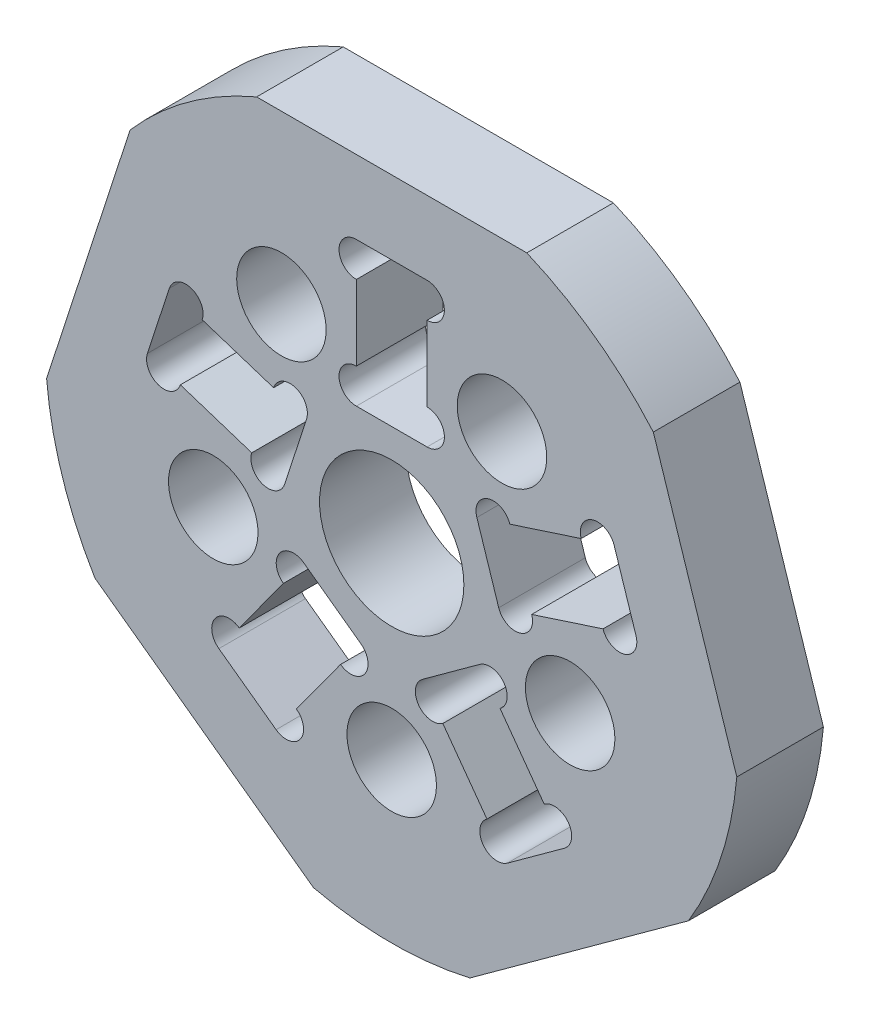
SolidWorks part; units mm, degrees
ref_plane "前视基准面" through (0, 0, 0) normal (0, 0, 1) x (1, 0, 0)
ref_plane "上视基准面" through (0, 0, 0) normal (0, 1, 0) x (1, 0, 0)
ref_plane "右视基准面" through (0, 0, 0) normal (1, 0, 0) x (0, 0, -1)
sketch "草图1" plane through (0, 0, 0) normal (0, 0, 1) x (1, 0, 0)
  circle A0 centre (0, 0) radius 12
  dimension "D1" = 24
extrude "凸台-拉伸1" add sketch "草图1" along normal mid plane 3
sketch "草图2" plane through (0, 0, 1.5) normal (0, 0, 1) x (1, 0, 0)
  line L1 (1.225, 3.5) -> (-1.225, 3.5)
  line L2 (1.225, 3.5) -> (1.225, 8.5)
  line L3 (1.225, 8.5) -> (-1.225, 8.5)
  line L4 (-1.225, 3.5) -> (-1.225, 8.5)
  line L5 (1.225, 3.5) -> (-1.225, 8.5) construction
  line L6 (1.225, 8.5) -> (-1.225, 3.5) construction
  circle A0 centre (0, -6.5) radius 1.55
  circle A1 centre (0, 0) radius 6.5 construction
  circle A2 centre (0, 0) radius 6 construction
  point P6 (0, 6)
  dimension "D1" = 13
  dimension "D2" = 3.1
  dimension "D5" = 12
  dimension "D3" = 2.45
  dimension "D4" = 5
extrude "切除-拉伸1" cut sketch "草图2" against normal through all
pattern_circular "阵列(圆周)1" count 5 over 360 about axis through (0, 0, 0) along (0, 0, 1) of "切除-拉伸1"
sketch "草图3" plane through (0, 0, 1.5) normal (0, 0, 1) x (1, 0, 0)
  line L0 (1.225, 3.5) -> (1.225, 8.5) construction
  line L1 (-1.225, 8.5) -> (-1.225, 3.5) construction
  circle A0 centre (1.225, 7.9) radius 0.6
  circle A1 centre (-1.225, 7.9) radius 0.6
  circle A2 centre (-1.225, 4.1) radius 0.6
  circle A3 centre (1.225, 4.1) radius 0.6
  dimension "D1" = 1.2
extrude "切除-拉伸2" cut sketch "草图3" against normal through all
pattern_circular "阵列(圆周)2" count 5 over 360 about axis through (0, 0, 0) along (0, 0, 1) of "切除-拉伸2"
sketch "草图4" plane through (0, 0, 1.5) normal (0, 0, 1) x (1, 0, 0)
  circle A0 centre (0, 0) radius 2.5
  dimension "D1" = 5
extrude "切除-拉伸3" cut sketch "草图4" against normal through all
sketch "草图5" plane through (0, 0, 1.5) normal (0, 0, 1) x (1, 0, 0)
  line L0 (-4.6795, 11.05) -> (4.6795, 11.05)
  line L1 (1.225, 8.5) -> (-1.225, 8.5) construction
  circle A0 centre (0, 0) radius 12 construction
  arc A1 (4.6795, 11.05) -> (-4.6795, 11.05) centre (0, 0) ccw
  dimension "D1" = 2.55
extrude "切除-拉伸4" cut sketch "草图5" against normal through all
pattern_circular "阵列(圆周)3" count 5 over 360 about axis through (0, 0, 0) along (0, 0, 1) of "切除-拉伸4"
